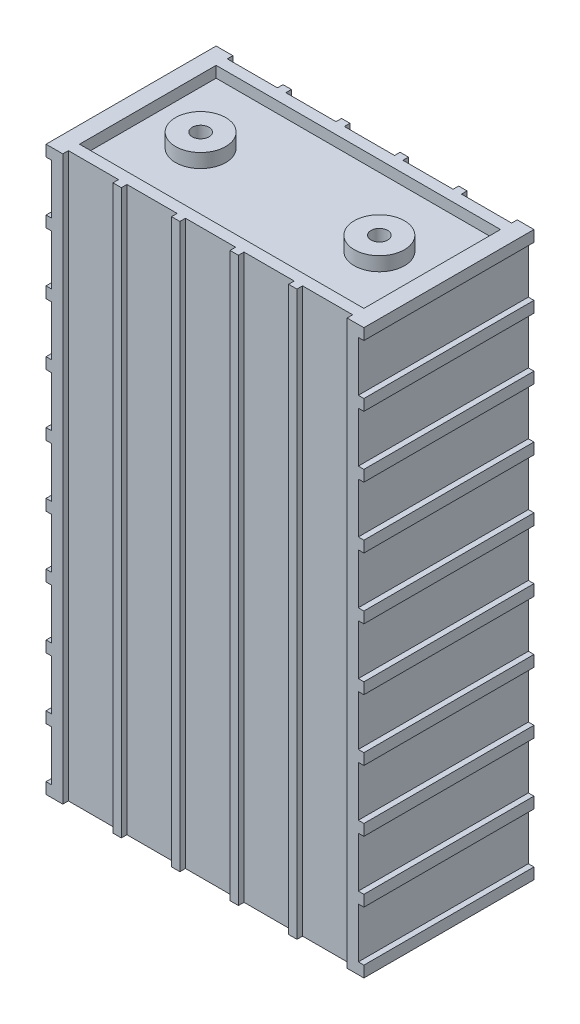
SolidWorks part; units mm, degrees
ref_plane "Alzado" through (0, 0, 0) normal (0, 0, 1) x (1, 0, 0)
ref_plane "Planta" through (0, 0, 0) normal (0, 1, 0) x (1, 0, 0)
ref_plane "Vista lateral" through (0, 0, 0) normal (1, 0, 0) x (0, 0, -1)
sketch "Croquis1" plane through (0, 0, 0) normal (0, 0, 1) x (1, 0, 0)
  line L1 (-57, 101) -> (57, 101)
  line L2 (-57, 101) -> (-57, -101)
  line L3 (-57, -101) -> (57, -101)
  line L4 (57, 101) -> (57, -101)
  line L5 (-57, 101) -> (57, -101) construction
  line L6 (-57, -101) -> (57, 101) construction
  point P0 (0, 0)
  dimension "D1" = 202
  dimension "D2" = 114
extrude "Saliente-Extruir1" add sketch "Croquis1" along normal mid plane 61
sketch "Croquis2" plane through (0, 0, 30.5) normal (0, 0, 1) x (1, 0, 0)
  line L0 (57, -101) -> (57, 101) construction
  line L1 (57, 97) -> (55, 97)
  line L2 (57, 97) -> (57, 79)
  line L3 (57, 79) -> (55, 79)
  line L4 (55, 97) -> (55, 79)
  line L5 (57, 97) -> (55, 79) construction
  line L6 (57, 79) -> (55, 97) construction
  line L7 (57, 101) -> (-57, 101) construction
  point P4 (56, 88)
  dimension "D1" = 4
  dimension "D2" = 2
  dimension "D3" = 18
extrude "Cortar-Extruir1" cut sketch "Croquis2" against normal through all
pattern_linear "MatrizL1" count 9 spacing 22 along (0, -1, 0) of "Cortar-Extruir1"
mirror "Simetría1" about plane through (0, 0, 0) normal (1, 0, 0) of "MatrizL1", "Cortar-Extruir1"
sketch "Croquis3" plane through (0, 101, 0) normal (0, 1, 0) x (1, 0, 0)
  line L0 (0, 0) -> (0, 50000) construction
  line L1 (57, 30.5) -> (-57, 30.5) construction
  line L2 (-9, 28.5) -> (9, 28.5)
  line L3 (-9, 28.5) -> (-9, 30.5)
  line L4 (-9, 30.5) -> (9, 30.5)
  line L5 (9, 28.5) -> (9, 30.5)
  line L6 (-9, 28.5) -> (9, 30.5) construction
  line L7 (-9, 30.5) -> (9, 28.5) construction
  line L8 (9, 28.5) -> (12, 28.5) construction
  line L9 (12, 30.5) -> (30, 30.5)
  line L10 (12, 30.5) -> (12, 28.5)
  line L11 (12, 28.5) -> (30, 28.5)
  line L12 (30, 30.5) -> (30, 28.5)
  line L13 (12, 30.5) -> (30, 28.5) construction
  line L14 (12, 28.5) -> (30, 30.5) construction
  line L15 (33, 30.5) -> (51, 30.5)
  line L16 (33, 30.5) -> (33, 28.5)
  line L17 (33, 28.5) -> (51, 28.5)
  line L18 (51, 30.5) -> (51, 28.5)
  line L19 (33, 30.5) -> (51, 28.5) construction
  line L20 (33, 28.5) -> (51, 30.5) construction
  line L21 (30, 28.5) -> (33, 28.5) construction
  line L22 (-30, 28.5) -> (-33, 28.5) construction
  line L23 (-33, 28.5) -> (-51, 30.5) construction
  line L24 (-33, 30.5) -> (-51, 28.5) construction
  line L25 (-12, 28.5) -> (-30, 30.5) construction
  line L26 (-12, 30.5) -> (-30, 28.5) construction
  line L27 (-9, 28.5) -> (-12, 28.5) construction
  line L28 (-51, 30.5) -> (-51, 28.5)
  line L29 (-33, 28.5) -> (-51, 28.5)
  line L30 (-33, 30.5) -> (-33, 28.5)
  line L31 (-33, 30.5) -> (-51, 30.5)
  line L32 (-30, 30.5) -> (-30, 28.5)
  line L33 (-12, 28.5) -> (-30, 28.5)
  line L34 (-12, 30.5) -> (-12, 28.5)
  line L35 (-12, 30.5) -> (-30, 30.5)
  point P3 (0, 29.5)
  point P14 (21, 29.5)
  point P19 (42, 29.5)
  point P28 (-42, 29.5)
  point P29 (-21, 29.5)
  dimension "D1" = 2
  dimension "D2" = 18
  dimension "D3" = 3
extrude "Cortar-Extruir2" cut sketch "Croquis3" against normal through all
mirror "Simetría2" about plane through (0, 0, 0) normal (0, 0, 1) of "Cortar-Extruir2"
sketch "Croquis4" plane through (0, 101, 0) normal (0, 1, 0) x (1, 0, 0)
  line L0 (57, -30.5) -> (57, 30.5) construction
  line L1 (-51, -24.5) -> (51, -24.5)
  line L2 (-51, -24.5) -> (-51, 24.5)
  line L3 (-51, 24.5) -> (51, 24.5)
  line L4 (51, -24.5) -> (51, 24.5)
  line L5 (-51, -24.5) -> (51, 24.5) construction
  line L6 (-51, 24.5) -> (51, -24.5) construction
  line L7 (57, 30.5) -> (51, 30.5) construction
  point P0 (0, 0)
  dimension "D1" = 6
  dimension "D2" = 6
extrude "Cortar-Extruir3" cut sketch "Croquis4" against normal blind 4
sketch "Croquis5" plane through (0, 97, 0) normal (0, 1, 0) x (1, 0, 0)
  line L0 (0, 0) -> (50000, 0) construction
  circle A0 centre (32.0532, 0) radius 9
  dimension "D1" = 18
extrude "Saliente-Extruir2" add sketch "Croquis5" along normal blind 5
sketch "Croquis6" plane through (0, 102, 0) normal (0, 1, 0) x (1, 0, 0)
  line L0 (0, 0) -> (50000, 0) construction
  circle A0 centre (32.0532, 0) radius 3
  dimension "D1" = 6
extrude "Cortar-Extruir4" cut sketch "Croquis6" against normal blind 10
mirror "Simetría4" about plane through (0, 0, 0) normal (1, 0, 0) of "Cortar-Extruir4", "Saliente-Extruir2"
